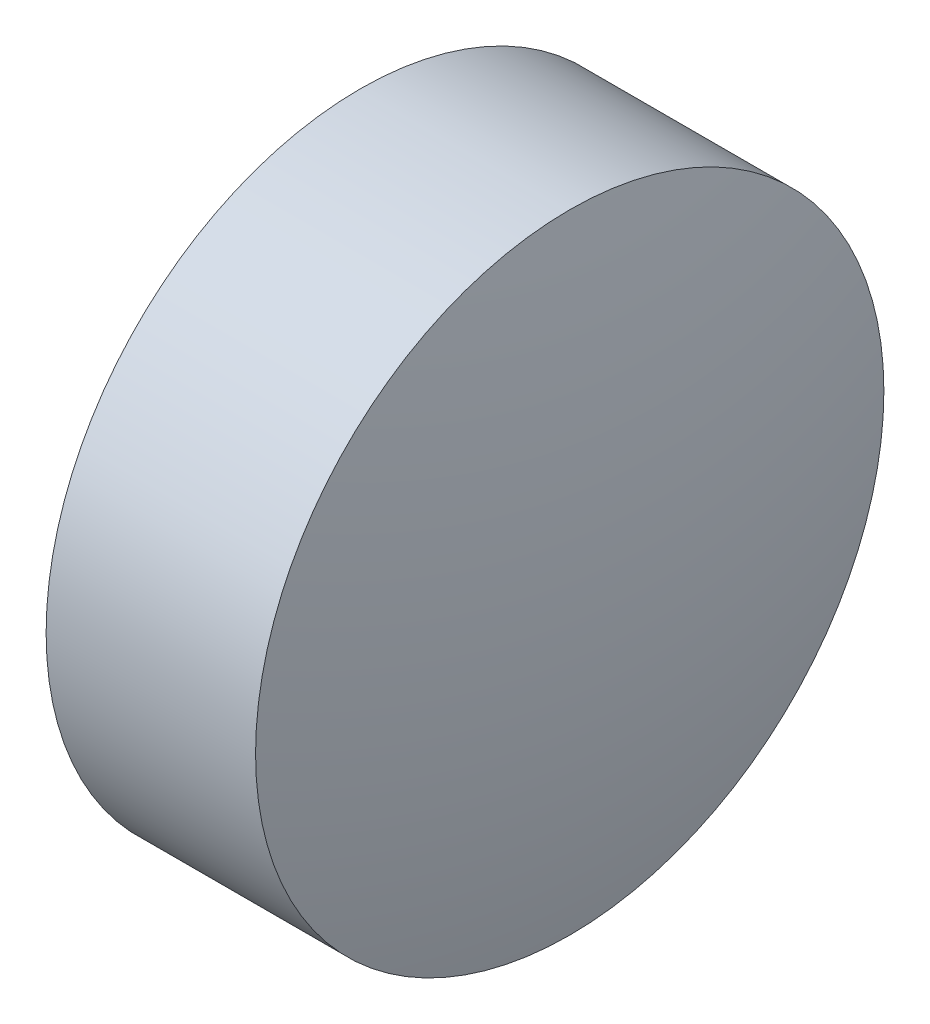
SolidWorks part; units mm, degrees
ref_plane "前视基准面" through (0, 0, 0) normal (0, 0, 1) x (1, 0, 0)
ref_plane "上视基准面" through (0, 0, 0) normal (0, 1, 0) x (1, 0, 0)
ref_plane "右视基准面" through (0, 0, 0) normal (1, 0, 0) x (0, 0, -1)
sketch "草图2" plane through (0, 0, 0) normal (0, 0, 1) x (1, 0, 0)
  line L0 (9.7117, 7.2421) -> (10.7117, 7.2421)
  line L1 (10.7117, 7.2421) -> (10.7117, 4.2421)
  line L2 (10.7117, 4.2421) -> (9.7117, 4.2421)
  line L3 (9.7117, 4.2421) -> (9.7117, 7.2421)
  line L4 (9.2876, 5.7421) -> (11.1558, 5.7421) construction
  arc A0 (9.7117, 7.2421) -> (9.7117, 4.2421) centre (15.875, 5.7421) ccw
  arc A1 (10.7117, 4.2421) -> (10.7117, 7.2421) centre (4.5483, 5.7421) ccw
  dimension "D1" = 1
  dimension "D2" = 3
revolve "旋转1" add sketch "草图2" angle 360 about L4
